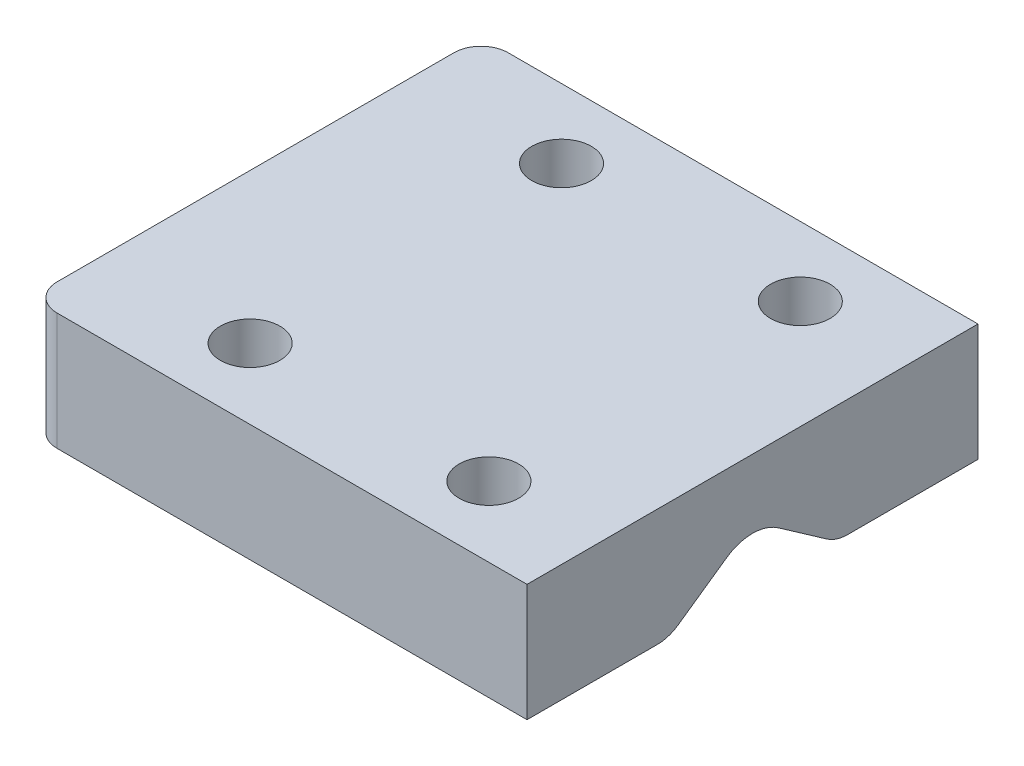
SolidWorks part; units mm, degrees
ref_plane "Front Plane" through (0, 0, 0) normal (0, 0, 1) x (1, 0, 0)
ref_plane "Top Plane" through (0, 0, 0) normal (0, 1, 0) x (1, 0, 0)
ref_plane "Right Plane" through (0, 0, 0) normal (1, 0, 0) x (0, 0, -1)
sketch "Sketch6" plane through (0, 68, 0) normal (0, 1, 0) x (1, 0, 0)
  line L1 (27.5, 25) -> (-27.5972, 25)
  line L2 (27.5, 25) -> (27.5, -25)
  line L3 (27.5, -25) -> (-27.5972, -25)
  line L4 (-27.5972, 25) -> (-27.5972, -25)
  line L5 (-24.5, -25) -> (27.5, -25) construction
extrude "Main Body" add sketch "Sketch6" along normal blind 13
sketch "Sketch7" plane through (27.5, 0, 0) normal (1, 0, 0) x (0, 0, -1)
  line L0 (0, 74.5) -> (-9.283, 68)
  line L1 (-25, 68) -> (25, 68) construction
  line L3 (0, 74.5) -> (9.283, 68)
  line L4 (9.283, 68) -> (0, 61.5)
  line L5 (0, 61.5) -> (-9.283, 68)
  line L6 (0, 74.5) -> (0, 61.5) construction
  dimension "D1" = 110
  dimension "D2" = 13
extrude "Main Hole" cut sketch "Sketch7" against normal through all
fillet "Exterior Fillet" radius 3 2 edges at (-27.5972, 74.5, -25) (-27.5972, 74.5, 25)
sketch "Sketch9" plane through (0, 81, 0) normal (0, 1, 0) x (1, 0, 0)
  circle A0 centre (15.4737, -17.2012) radius 3.3
  circle A1 centre (-11, -17.2012) radius 3.3
  circle A2 centre (15.4737, 17.3243) radius 3.3
  circle A3 centre (-11, 17.3243) radius 3.3
extrude "Bolt Holes" cut sketch "Sketch9" against normal through all
fillet "Top Hole Fillet" radius 5 1 edges at (-0.0486, 74.5, 0)
fillet "Side Hole Fillet" radius 4 2 edges at (-0.0486, 68, -9.283) (-0.0486, 68, 9.283)
